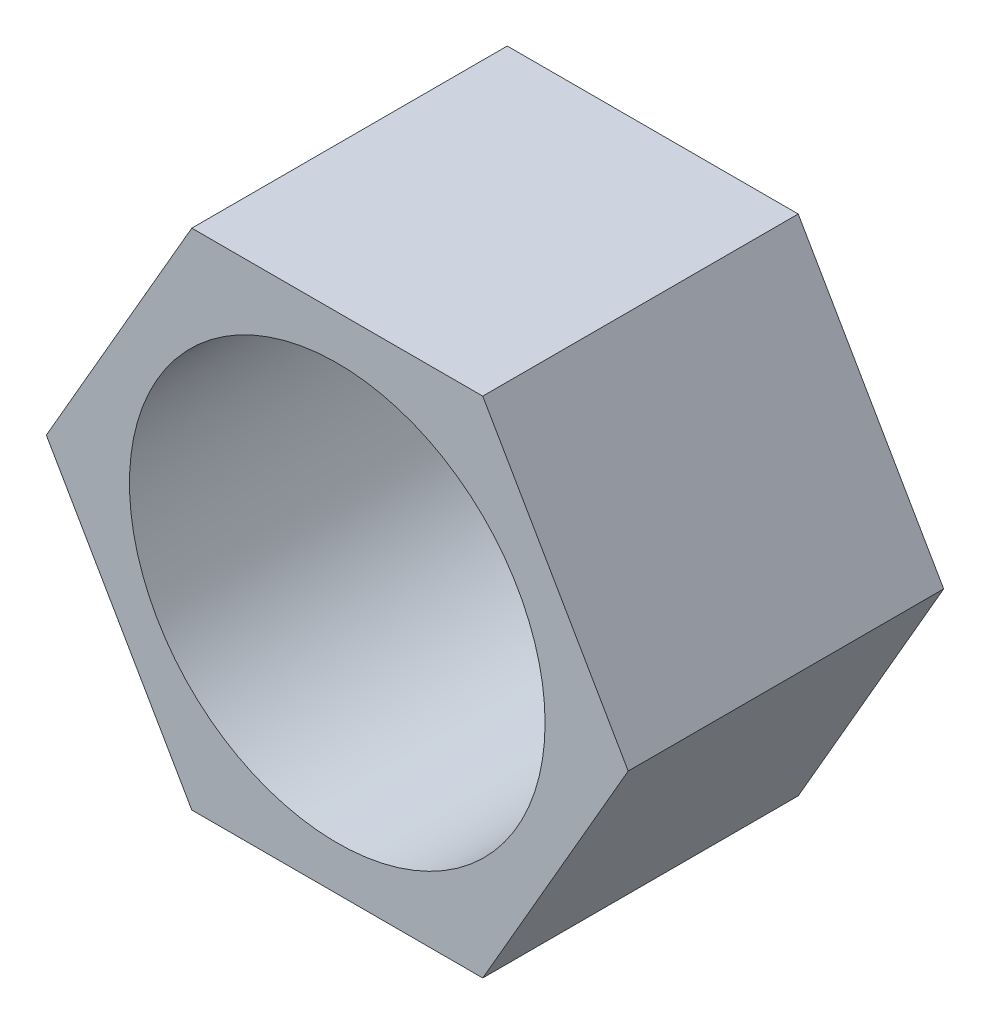
SolidWorks part; units mm, degrees
ref_plane "Front Plane" through (0, 0, 0) normal (0, 0, 1) x (1, 0, 0)
ref_plane "Top Plane" through (0, 0, 0) normal (0, 1, 0) x (1, 0, 0)
ref_plane "Right Plane" through (0, 0, 0) normal (1, 0, 0) x (0, 0, -1)
sketch "Sketch2" plane through (0, 0, 0) normal (0, 0, 1) x (1, 0, 0)
  line L2 (7, 0) -> (3.5, 6.0622)
  line L3 (3.5, 6.0622) -> (-3.5, 6.0622)
  line L4 (-3.5, 6.0622) -> (-7, 0)
  line L5 (-7, 0) -> (-3.5, -6.0622)
  line L6 (-3.5, -6.0622) -> (3.5, -6.0622)
  line L7 (3.5, -6.0622) -> (7, 0)
  circle A0 centre (0, 0) radius 7 construction
  circle A1 centre (0, 0) radius 5
  dimension "D1" = 14
  dimension "D2" = 10
extrude "Boss-Extrude1" add sketch "Sketch2" along normal blind 7.59
